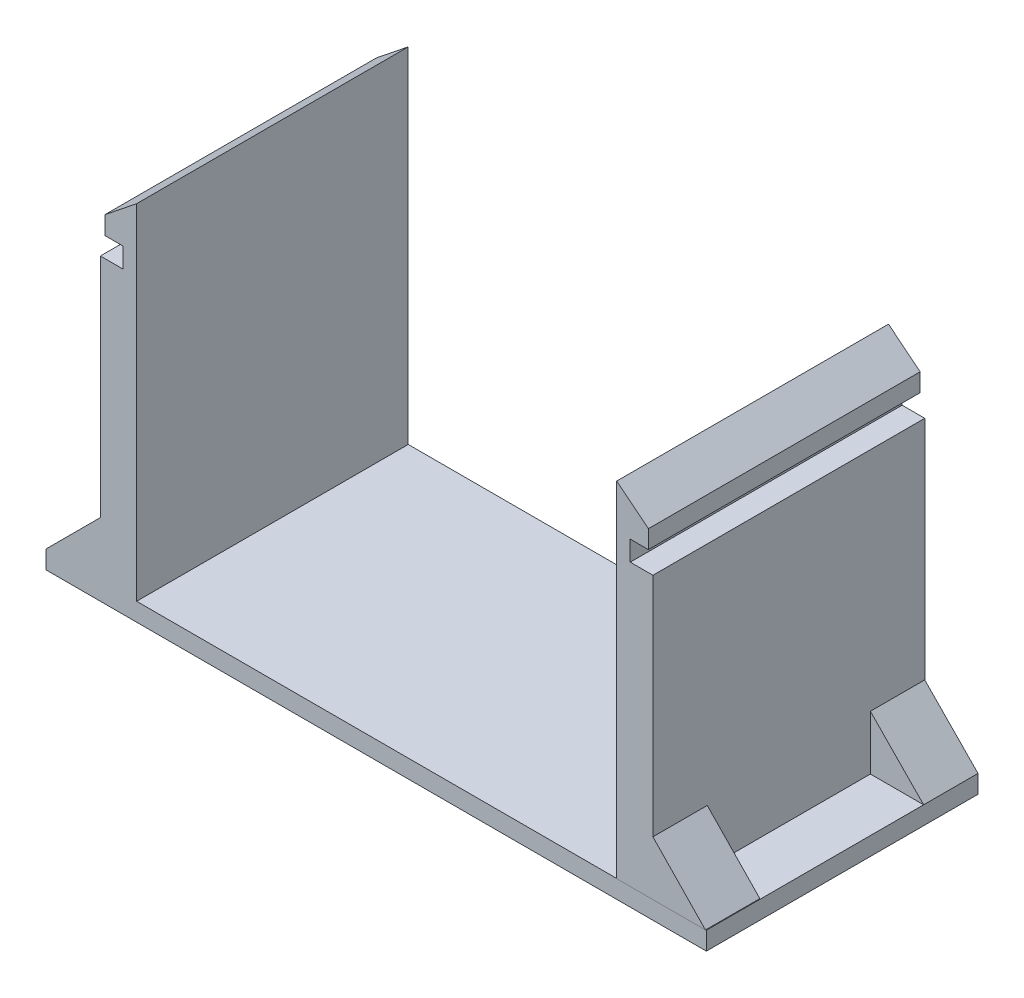
SolidWorks part; units mm, degrees
ref_plane "Front Plane" through (0, 0, 0) normal (0, 0, 1) x (1, 0, 0)
ref_plane "Top Plane" through (0, 0, 0) normal (0, 1, 0) x (1, 0, 0)
ref_plane "Right Plane" through (0, 0, 0) normal (1, 0, 0) x (0, 0, -1)
sketch "Sketch2" plane through (0, 0, 0) normal (0, 1, 0) x (1, 0, 0)
  line L0 (35.6824, 11.9311) -> (31.6824, 11.9311)
  line L1 (-26.1176, 11.9311) -> (38.8824, 11.9311)
  line L2 (-26.1176, 11.9311) -> (-26.1176, -18.0689)
  line L3 (-26.1176, -18.0689) -> (38.8824, -18.0689)
  line L4 (38.8824, 11.9311) -> (38.8824, -18.0689)
  line L5 (-24.1176, 11.9311) -> (-20.1176, 11.9311)
  line L6 (-24.1176, 11.9311) -> (-24.1176, -18.0444)
  line L7 (35.6824, -18.1495) -> (31.6824, -18.1495)
  line L8 (-20.1176, 11.9311) -> (-20.1176, -18.0444)
  line L9 (-24.1176, -18.0444) -> (-20.1176, -18.0444)
  line L10 (32.8824, 11.9311) -> (36.8824, 11.9311)
  line L11 (32.8824, 11.9311) -> (32.8824, -18.2546)
  line L12 (36.8824, 11.9311) -> (36.8824, -18.2546)
  line L13 (32.8824, -18.2546) -> (36.8824, -18.2546)
  point P4 (6.3824, -3.0689)
  point P5 (32.8824, -3.0689)
  point P6 (-20.1176, -3.0689)
  point P7 (-20.1176, 11.9311)
  point P8 (32.8824, 11.9311)
  point P9 (-24.1176, 11.9311)
  point P10 (36.8824, 11.9311)
  dimension "D1" = 30
  dimension "D2" = 65
  dimension "D3" = 15
  dimension "D4" = 26.5
  dimension "D5" = 26.5
  dimension "D6" = 4
  dimension "D7" = 4
extrude "Boss-Extrude1" add sketch "Sketch2" along normal blind 38 contours L6 L9 L8 L1 | L12 L1 L0 L11 L3
sketch "Sketch3" plane through (0, 0, 0) normal (0, 1, 0) x (1, 0, 0)
  line L0 (-24.1176, 11.9311) -> (-20.1176, 11.9311) construction
  line L1 (-24.1176, -18.0444) -> (-20.1176, -18.0444) construction
  line L2 (32.8824, 11.9311) -> (36.8824, 11.9311) construction
  line L3 (32.8824, -18.0689) -> (36.8824, -18.0689) construction
  line L4 (-30.1176, -18.0444) -> (-30.1176, 11.9311)
  line L5 (-30.1176, -18.0444) -> (42.7587, -18.0444)
  line L6 (-30.1176, 11.9311) -> (42.7587, 11.9311)
  line L7 (42.7587, -18.0444) -> (42.7587, 11.9311)
  point P0 (-20.1176, 11.9311)
  point P1 (-30.1176, 11.9311)
  point P3 (-20.1176, -18.0444)
  point P6 (-30.1176, -18.0444)
  point P8 (-3.6019, -1.4573)
  point P11 (32.8824, 11.9311)
  point P12 (42.8824, 11.9311)
  point P14 (32.8824, -18.0689)
  point P17 (42.8824, -18.0689)
  dimension "D1" = 10
  dimension "D2" = 10
  dimension "D3" = 10
  dimension "D4" = 10
extrude "Boss-Extrude3" add sketch "Sketch3" against normal blind 2
sketch "Sketch6" plane through (0, 0, 18.0689) normal (0, 0, 1) x (1, 0, 0)
  line L0 (36.8824, 38) -> (36.8824, 0) construction
  line L1 (36.8824, 6) -> (36.8824, 0)
  line L2 (36.8824, 0) -> (42.6824, 0)
  line L3 (42.6824, 0) -> (36.8824, 6)
  point P0 (36.8824, 6)
  point P1 (42.6824, 0)
  dimension "D1" = 6
  dimension "D2" = 5.8
extrude "Boss-Extrude4" add sketch "Sketch6" against normal blind 6
sketch "Sketch7" plane through (0, 0, -11.9311) normal (0, 0, -1) x (-1, 0, 0)
  line L0 (-36.8824, 38) -> (-36.8824, 0) construction
  line L1 (-42.7587, 0) -> (-36.8824, 6)
  line L2 (-36.8824, 6) -> (-36.8824, 0)
  line L3 (-36.8824, 0) -> (-42.7587, 0)
  point P0 (-42.7587, 0)
  point P1 (-36.8824, 6)
  dimension "D1" = 6
extrude "Boss-Extrude5" add sketch "Sketch7" against normal blind 6
sketch "Sketch8" plane through (0, 0, -11.9311) normal (0, 0, -1) x (-1, 0, 0)
  line L0 (24.1176, 38) -> (24.1176, 0) construction
  line L1 (24.1176, 6) -> (24.1176, 0)
  line L2 (24.1176, 0) -> (30.1176, 0)
  line L3 (30.1176, 0) -> (24.1176, 6)
  point P0 (24.1176, 6)
  point P1 (30.1176, 0)
  dimension "D1" = 6
sketch "Sketch9" plane through (0, 0, 18.0444) normal (0, 0, 1) x (1, 0, 0)
  line L0 (-24.1176, 38) -> (-24.1176, 0) construction
  line L1 (-24.1176, 6) -> (-30.1176, 0)
  line L2 (-30.1176, 0) -> (-24.1176, 0)
  line L3 (-24.1176, 0) -> (-24.1176, 6)
  point P0 (-30.1176, 0)
  point P1 (-24.1176, 6)
  dimension "D1" = 6
  dimension "D2" = 6
extrude "Boss-Extrude7" add sketch "Sketch9" against normal blind 6
extrude "Boss-Extrude8" add sketch "Sketch8" against normal blind 6
sketch "Sketch17" plane through (36.8824, 0, 0) normal (1, 0, 0) x (0, 0, -1)
  line L0 (5.9311, 0) -> (-12.0689, 0) construction
  line L1 (11.9311, 38) -> (11.9311, 6) construction
  line L2 (11.9311, 31) -> (11.9311, 38)
  line L3 (11.9311, 31) -> (-20.7862, 31)
  line L4 (11.9311, 38) -> (-20.7862, 38)
  line L5 (-20.7862, 31) -> (-20.7862, 38)
  point P0 (-3.0689, 0)
  point P1 (-3.0689, 31)
  point P4 (11.9311, 31)
  dimension "D1" = 31
extrude "Cut-Extrude9" cut sketch "Sketch17" against normal blind 0.5
sketch "Sketch18" plane through (36.3824, 0, 0) normal (1, 0, 0) x (0, 0, -1)
  line L0 (-18.0689, 31) -> (-18.0689, 38) construction
  line L1 (11.9311, 31) -> (11.9311, 38) construction
  line L2 (-18.0689, 33.2) -> (-18.0689, 31)
  line L3 (-18.0689, 33.2) -> (22.0308, 33.2)
  line L4 (-18.0689, 31) -> (22.0308, 31)
  line L5 (22.0308, 33.2) -> (22.0308, 31)
  point P0 (-18.0689, 33.2)
  point P1 (11.9311, 33.2)
  dimension "D1" = 2.2
  dimension "D2" = 2.2
extrude "Cut-Extrude10" cut sketch "Sketch18" against normal blind 2
sketch "Sketch19" plane through (0, 0, 18.0689) normal (0, 0, 1) x (1, 0, 0)
  line L0 (36.3824, 33.2) -> (36.3824, 38) construction
  line L1 (36.3824, 35.2) -> (32.8824, 38)
  line L2 (32.8824, 38) -> (30.8185, 44.9078)
  line L3 (30.8185, 44.9078) -> (43.4658, 41.1621)
  line L4 (43.4658, 41.1621) -> (36.3824, 35.2)
  point P0 (36.3824, 35.2)
  dimension "D1" = 2
extrude "Cut-Extrude11" cut sketch "Sketch19" against normal through all
sketch "Sketch20" plane through (-24.1176, 0, 0) normal (-1, 0, 0) x (0, 0, 1)
  line L0 (-5.9311, 0) -> (12.0444, 0) construction
  line L1 (18.0444, 38) -> (18.0444, 6) construction
  line L2 (18.0444, 31) -> (18.0444, 41.95)
  line L3 (18.0444, 31) -> (-31.1724, 31)
  line L4 (18.0444, 41.95) -> (-31.1724, 41.95)
  line L5 (-31.1724, 31) -> (-31.1724, 41.95)
  point P0 (3.0566, 0)
  point P1 (3.0566, 31)
  point P4 (18.0444, 31)
  dimension "D1" = 31
extrude "Cut-Extrude12" cut sketch "Sketch20" against normal blind 0.5
sketch "Sketch21" plane through (-23.6176, 0, 0) normal (-1, 0, 0) x (0, 0, 1)
  line L0 (18.0444, 31) -> (18.0444, 38) construction
  line L1 (-11.9311, 38) -> (-11.9311, 31) construction
  line L2 (18.0444, 33.2) -> (18.0444, 31)
  line L3 (18.0444, 33.2) -> (-24.4996, 33.2)
  line L4 (18.0444, 31) -> (-24.4996, 31)
  line L5 (-24.4996, 33.2) -> (-24.4996, 31)
  point P0 (18.0444, 33.2)
  point P1 (-11.9311, 33.2)
  dimension "D1" = 2.2
  dimension "D2" = 2.2
extrude "Cut-Extrude13" cut sketch "Sketch21" against normal blind 2
sketch "Sketch22" plane through (0, 0, 18.0444) normal (0, 0, 1) x (1, 0, 0)
  line L0 (-23.6176, 33.2) -> (-23.6176, 38) construction
  line L1 (-23.6176, 35.2) -> (-20.1176, 38)
  line L2 (-20.1176, 38) -> (-17.3086, 46.7)
  line L3 (-17.3086, 46.7) -> (-43.9495, 46.7)
  line L4 (-43.9495, 46.7) -> (-33.8495, 36.6)
  line L5 (-33.8495, 36.6) -> (-23.6176, 35.2)
  point P0 (-23.6176, 35.2)
  dimension "D1" = 2
extrude "Cut-Extrude14" cut sketch "Sketch22" against normal through all
